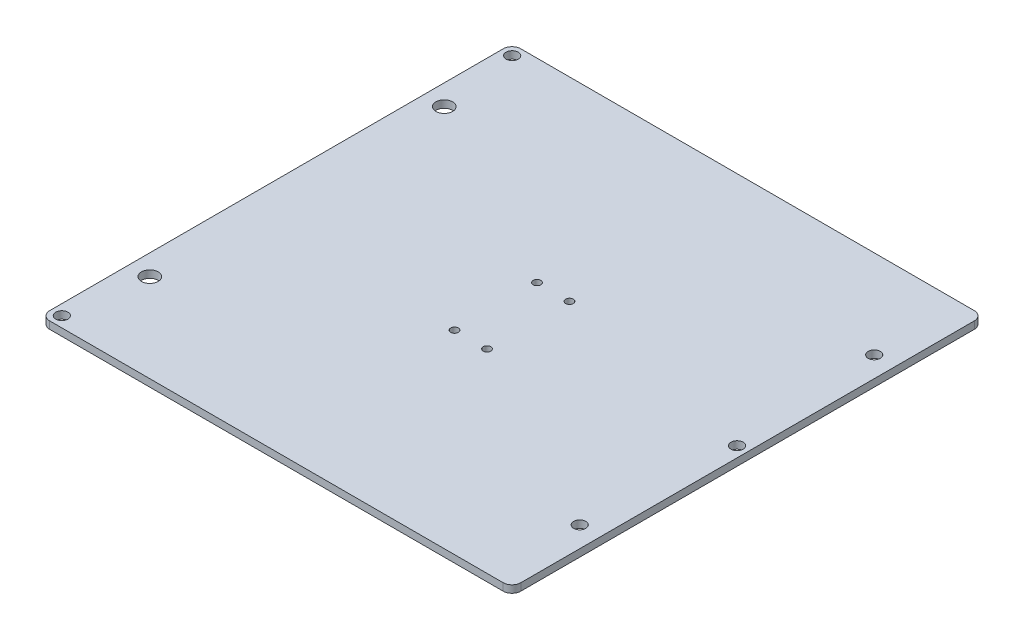
SolidWorks part; units mm, degrees
material "5052-H32"
ref_plane "Front Plane" through (0, 0, 0) normal (0, 0, 1) x (1, 0, 0)
ref_plane "Top Plane" through (0, 0, 0) normal (0, 1, 0) x (1, 0, 0)
ref_plane "Right Plane" through (0, 0, 0) normal (1, 0, 0) x (0, 0, -1)
sketch "Sketch1" plane through (0, 0, 0) normal (0, 1, 0) x (1, 0, 0)
  line L0 (0, 0) -> (203.2, 0)
  line L1 (0, 0) -> (203.2, 0) construction
  line L2 (0, 0) -> (0, 203.2)
  line L3 (0, 203.2) -> (203.2, 203.2)
  line L4 (203.2, 0) -> (203.2, 203.2)
  line L5 (0, 0) -> (203.2, 0) construction
  dimension "D1" = 203.2
  dimension "D2" = 203.2
extrude "Boss-Extrude1" add sketch "Sketch1" along normal blind 3.175
sketch "Sketch2" plane through (0, 3.175, 0) normal (0, 1, 0) x (1, 0, 0)
  line L0 (203.2, 203.2) -> (0, 203.2) construction
  line L1 (0, 0) -> (203.2, 0) construction
  line L2 (203.2, 203.2) -> (0, 203.2) construction
  line L4 (8.9014, 203.2) -> (8.9014, 0) construction
  line L5 (194.2986, 0) -> (194.2986, 203.2) construction
  line L7 (101.6, 203.2) -> (101.6, 0) construction
  circle A0 centre (8.9014, 38.1) radius 3.6
  circle A1 centre (8.9014, 165.1) radius 3.6
  circle A2 centre (194.2986, 38.1) radius 2.625
  circle A3 centre (194.2986, 165.1) radius 2.625
  dimension "D2" = 7.2
  dimension "D5" = 5.25
  dimension "D1" = 185.3971
  dimension "D3" = 38.1
  dimension "D4" = 38.1
extrude "wheel holes" cut sketch "Sketch2" against normal up to next
sketch "Sketch3" plane through (0, 0, 0) normal (0, -1, 0) x (1, 0, 0)
  line L0 (0, -203.2) -> (0, 0) construction
  line L2 (203.2, 0) -> (203.2, -203.2) construction
  line L4 (0, 0) -> (203.2, 0) construction
  circle A0 centre (4.5009, -4.572) radius 2.625
  circle A1 centre (4.5009, -198.7728) radius 2.625
  circle A2 centre (198.65, -101.6) radius 2.625
  dimension "D1" = 5.25
  dimension "D4" = 4.572
  dimension "D2" = 194.2008
  dimension "D3" = 4.5009
  dimension "D5" = 4.55
  dimension "D6" = 101.6
extrude "build plate holes" cut sketch "Sketch3" against normal up to next
fillet "Fillet1" radius 3.81 4 edges at (0, 1.5875, -203.2) (203.2, 1.5875, -203.2) (203.2, 1.5875, 0) (0, 1.5875, 0)
sketch "Sketch4" plane through (0, 3.175, 0) normal (0, 1, 0) x (1, 0, 0)
  line L0 (101.6, 0) -> (101.6, 203.2) construction
  line L3 (0, 101.6) -> (203.2, 101.6) construction
  line L6 (3.81, 0) -> (199.39, 0) construction
  line L7 (199.39, 203.2) -> (3.81, 203.2) construction
  line L8 (203.2, 3.81) -> (203.2, 199.39) construction
  circle A0 centre (94.6, 119.38) radius 1.65
  circle A1 centre (108.6, 119.38) radius 1.65
  circle A2 centre (108.6, 83.82) radius 1.65
  circle A3 centre (94.6, 83.82) radius 1.65
  dimension "D1" = 3.3
  dimension "D2" = 14
  dimension "D4" = 17.78
extrude "belt clamp holes" cut sketch "Sketch4" against normal up to next
